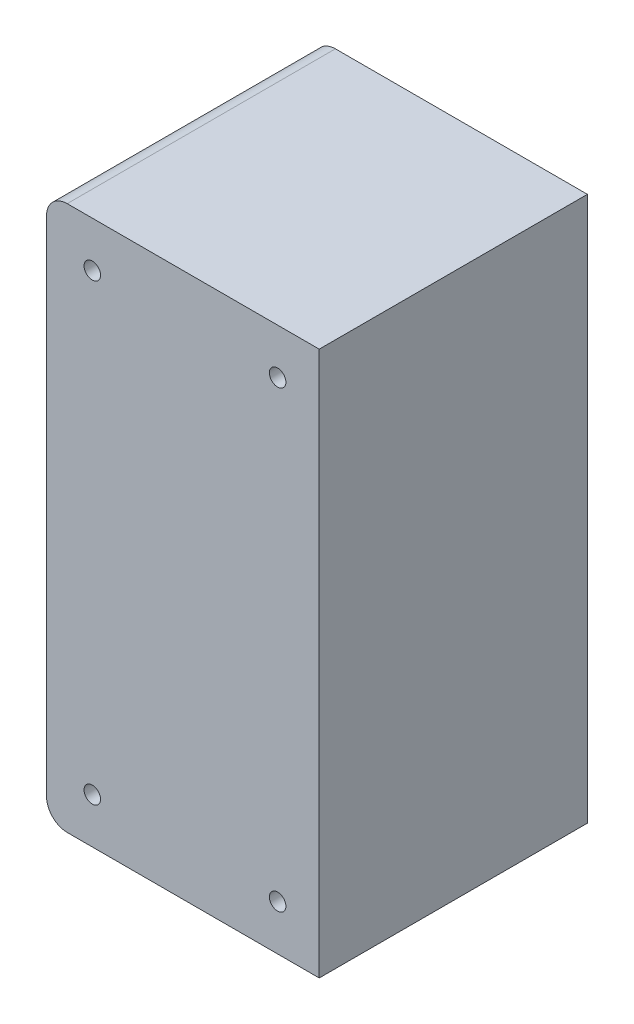
SolidWorks part; units mm, degrees
ref_plane "Front Plane" through (0, 0, 0) normal (0, 0, 1) x (1, 0, 0)
ref_plane "Top Plane" through (0, 0, 0) normal (0, 1, 0) x (1, 0, 0)
ref_plane "Right Plane" through (0, 0, 0) normal (1, 0, 0) x (0, 0, -1)
sketch "Sketch1" plane through (0, 0, 0) normal (0, 0, 1) x (1, 0, 0)
  line L0 (-33.042, 61) -> (-33.042, -61)
  line L1 (-28.042, -66) -> (33.042, -66)
  line L2 (33.042, -66) -> (33.042, 66)
  line L3 (33.042, 66) -> (-28.042, 66)
  circle A0 centre (22.958, -55) radius 2
  circle A1 centre (-21.958, 55) radius 2
  circle A2 centre (-21.958, -55) radius 2
  circle A3 centre (22.958, 55) radius 2
  arc A4 (-28.042, 66) -> (-33.042, 61) centre (-28.042, 61) ccw
  arc A5 (-33.042, -61) -> (-28.042, -66) centre (-28.042, -61) ccw
  dimension "D1" = 4
  dimension "D2" = 5
  dimension "D3" = 22.958
  dimension "D4" = 33.042
  dimension "D5" = 21.958
  dimension "D6" = 33.042
  dimension "D7" = 55
  dimension "D8" = 66
  dimension "D9" = 55
  dimension "D10" = 66
extrude "Boss-Extrude1" add sketch "Sketch1" along normal blind 65
shell "Shell1" thickness 4
sketch "Sketch2" plane through (0, 0, 0) normal (0, 0, -1) x (-1, 0, 0)
  circle A0 centre (-22.958, -55) radius 6 construction
  circle A1 centre (21.958, -55) radius 6 construction
  circle A2 centre (21.958, 55) radius 6 construction
  circle A3 centre (-22.958, 55) radius 6 construction
  circle A4 centre (-22.958, -55) radius 6
  circle A5 centre (21.958, -55) radius 6
  circle A6 centre (21.958, 55) radius 6
  circle A7 centre (-22.958, 55) radius 6
extrude "Cut-Extrude1" cut sketch "Sketch2" against normal blind 61
